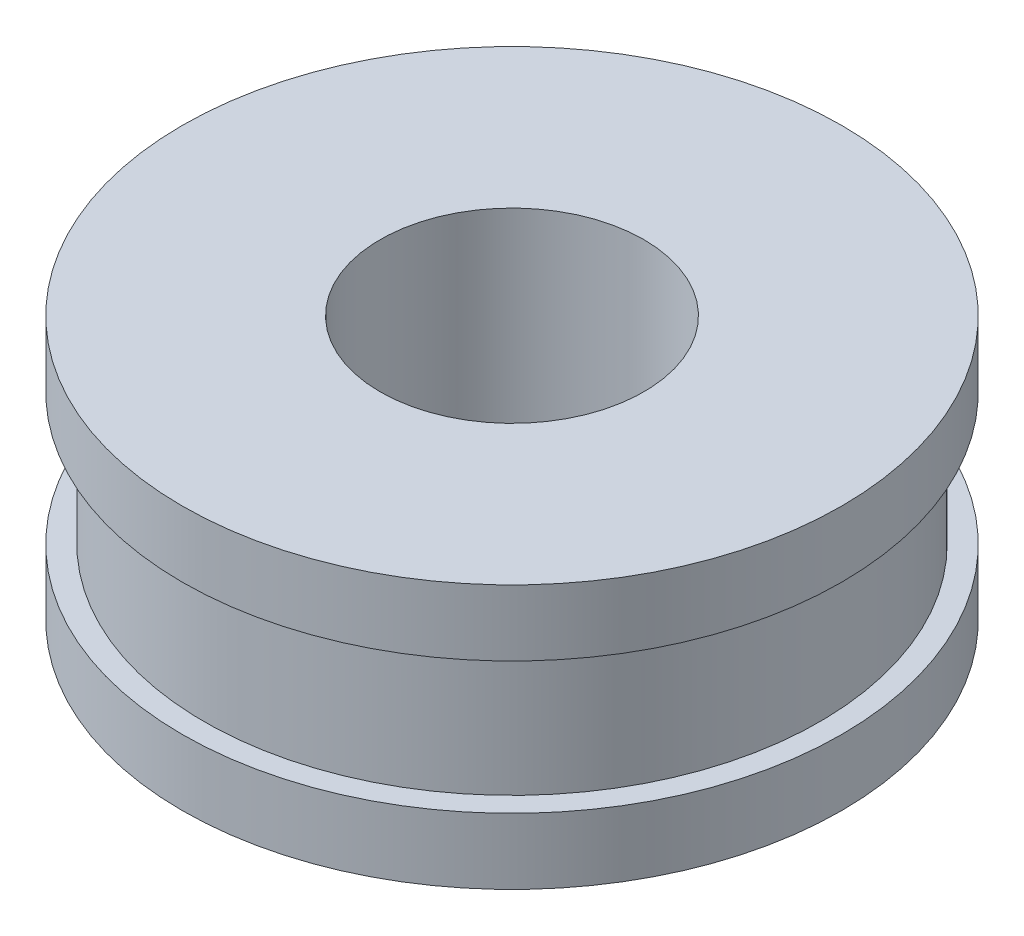
SolidWorks part; units mm, degrees
ref_plane "Front Plane" through (0, 0, 0) normal (0, 0, 1) x (1, 0, 0)
ref_plane "Top Plane" through (0, 0, 0) normal (0, 1, 0) x (1, 0, 0)
ref_plane "Right Plane" through (0, 0, 0) normal (1, 0, 0) x (0, 0, -1)
sketch "Sketch1" plane through (0, 0, 0) normal (0, 1, 0) x (1, 0, 0)
  circle A0 centre (0, 0) radius 7.5
  circle A1 centre (0, 0) radius 3
  dimension "D1" = 15
  dimension "D2" = 6
extrude "Boss-Extrude1" add sketch "Sketch1" along normal blind 6
sketch "Sketch2" plane through (0, 0, 0) normal (1, 0, 0) x (0, 0, -1)
  line L0 (7.5, 0) -> (7, 0) construction
  line L1 (-7.5, 0) -> (7.5, 0) construction
  line L2 (7, 0) -> (7, 1.5) construction
  line L3 (7.5, 1.5) -> (7, 1.5)
  line L4 (7.5, 0) -> (7.5, 6) construction
  line L5 (7, 1.5) -> (7, 4.5)
  line L6 (7, 4.5) -> (7.5, 4.5)
  line L7 (7.5, 4.5) -> (7.5, 1.5)
  line L8 (0, 0) -> (0, 6) construction
  line L9 (3, 6) -> (-3, 6) construction
  dimension "D1" = 0.5
  dimension "D2" = 1.5
  dimension "D3" = 3
revolve "Cut-Revolve1" cut sketch "Sketch2" angle 360 about L8
